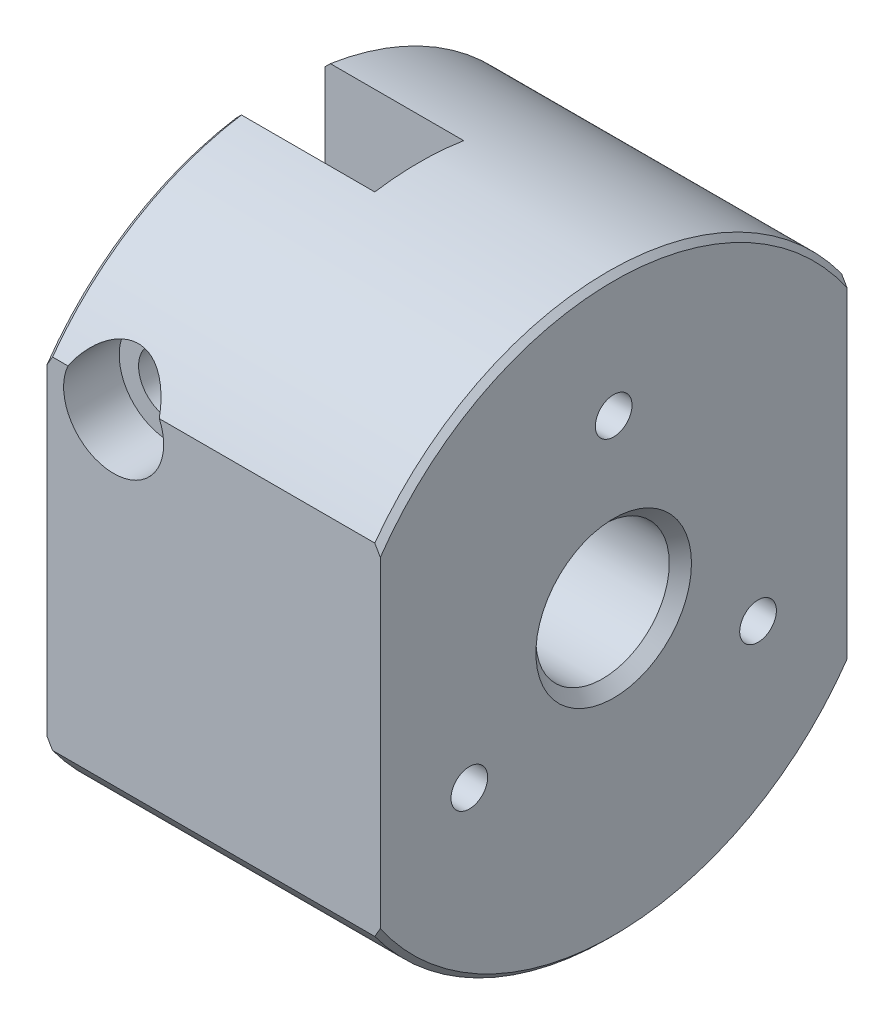
SolidWorks part; units mm, degrees
ref_plane "Front Plane" through (0, 0, 0) normal (0, 0, 1) x (1, 0, 0)
ref_plane "Top Plane" through (0, 0, 0) normal (0, 1, 0) x (1, 0, 0)
ref_plane "Right Plane" through (0, 0, 0) normal (1, 0, 0) x (0, 0, -1)
sketch "Sketch1" plane through (0, 0, 0) normal (1, 0, 0) x (0, 0, -1)
  line L0 (21, -15.3297) -> (21, 15.3297)
  line L1 (-21, 15.3297) -> (-21, -15.3297)
  arc A0 (21, 15.3297) -> (-21, 15.3297) centre (0, 0) ccw
  arc A1 (-21, -15.3297) -> (21, -15.3297) centre (0, 0) ccw
extrude "Boss-Extrude1" add sketch "Sketch1" against normal blind 30
sketch "Sketch2" plane through (-30, 0, 0) normal (-1, 0, 0) x (0, 0, 1)
  line L0 (-4, 25.6905) -> (-4, 4.4721)
  line L1 (4, 4.4721) -> (4, 25.6905)
  arc A0 (4, 25.6905) -> (-4, 25.6905) centre (0, 0) ccw
  arc A1 (-4, 4.4721) -> (4, 4.4721) centre (0, 0) cw
extrude "Cut-Extrude1" cut sketch "Sketch2" against normal blind 12.5
sketch "Sketch3" plane through (0, 0, 0) normal (0, 0, 1) x (1, 0, 0)
  line L0 (-30, 6) -> (-30, 0)
  line L1 (-30, 0) -> (0, 0)
  line L2 (0, 0) -> (0, 6)
  line L3 (0, 6) -> (-30, 6)
  line L4 (-30, 0) -> (0, 0) construction
revolve "Cut-Revolve1" cut sketch "Sketch3" angle 360 about L4
hole_wizard "Hole1" positions "Sketch5" profile "Sketch4" legacy
sketch "Sketch5" plane through (-17.5, 0, 0) normal (-1, 0, 0) x (0, 0, 1)
  point P0 (0, 21.2727)
sketch "Sketch4" plane through (-17.5, 21.2727, 0) normal (0, 1, 0) x (0, 0, 1)
  line L0 (0, 0) -> (0, 9.88)
  line L1 (0, 9.88) -> (2.54, 8.4135)
  line L2 (2.54, 8.4135) -> (2.54, 0)
  line L4 (2.54, 0) -> (0, 0)
  line L6 (0, 9.88) -> (-2.54, 8.4135) construction
  line L7 (0, -4.2442) -> (0, 117.3081) construction
  dimension "Diameter" = 5.08
  dimension "Depth" = 8.4135
  dimension "Drill Angle" = 120
hole_wizard "M3 Clearance Hole1" positions "Sketch7" profile "Sketch6" hole size "M3" standard "ANSI Metric"
sketch "Sketch7" plane through (0, 0, -4) normal (0, 0, 1) x (1, 0, 0)
  point P0 (-24, 13.5)
sketch "Sketch6" plane through (-24, 13.5, -4) normal (1, 0, 0) x (0, -1, 0)
  line L0 (0, 0) -> (0, 17)
  line L1 (0, 17) -> (1.621, 17)
  line L2 (1.621, 17) -> (1.621, 0)
  line L5 (1.621, 0) -> (0, 0)
  line L11 (0, -6.35) -> (0, 107.95) construction
  dimension "Thru Hole Dia." = 3.242
  dimension "Thru Hole Depth" = 17
hole_wizard "CBORE for M5 Hex Head Bolt1" positions "Sketch9" profile "Sketch8" counterbore size "M5" standard "ANSI Metric"
sketch "Sketch9" plane through (0, 0, 21) normal (0, 0, 1) x (1, 0, 0)
  point P0 (-24, 13.5)
sketch "Sketch8" plane through (-24, 13.5, 21) normal (1, 0, 0) x (0, -1, 0)
  line L0 (0, 0) -> (0, 17)
  line L1 (0, 17) -> (2.7559, 17)
  line L3 (2.7559, 17) -> (2.7559, 5)
  line L4 (2.7559, 5) -> (4.5, 5)
  line L5 (4.5, 5) -> (4.5, 0)
  line L7 (4.5, 0) -> (0, 0)
  line L11 (0, -6.35) -> (0, 107.95) construction
  dimension "Thru Hole Dia." = 5.5118
  dimension "Thru Hole Depth" = 17
  dimension "C'Bore Dia." = 9
  dimension "C'Bore Depth" = 5
chamfer "Chamfer1" distance 0.5 angle 45 5 edges at (-30, 22.2017, -13.5309) (0, 26, 0) (0, -26, 0) (-30, 22.2017, 13.5309) (-30, -26, 0)
chamfer "Chamfer2" distance 1 angle 45 2 edges at (0, 0, -6) (-30, -6, 0)
chamfer "Chamfer3" distance 0.379 angle 45 1 edges at (-22.379, 13.5, -4)
hole_wizard "M4 Tapped Hole1" positions "Sketch12" profile "Sketch13" tap size "M4" standard "ISO"
sketch "Sketch12" plane through (0, 0, 0) normal (1, 0, 0) x (0, 0, -1)
  point P0 (0, 15)
  point P9 (12.9904, -7.5)
  point P10 (-12.9904, -7.5)
  point P11 (0, 0)
  dimension "D1" = 15
  dimension "D2" = 3
cosmetic thread "Hole Thread1" parameters "D2"=4
cosmetic thread "Hole Thread2" parameters "D2"=4
cosmetic thread "Hole Thread3" parameters "D2"=4
sketch "Sketch13" plane through (0, 15, 0) normal (0, 1, 0) x (0, 0, -1)
  line L0 (0, 0) -> (0, 8.9914)
  line L1 (0, 8.9914) -> (1.65, 8)
  line L2 (1.65, 8) -> (1.65, 0)
  line L5 (1.65, 0) -> (0, 0)
  line L10 (0, 8.9914) -> (-1.65, 8) construction
  line L11 (0, -6.35) -> (0, 107.95) construction
  dimension "Tap Drill Dia." = 3.3
  dimension "Tap Drill Depth" = 8
  dimension "Drill Angle" = 118
